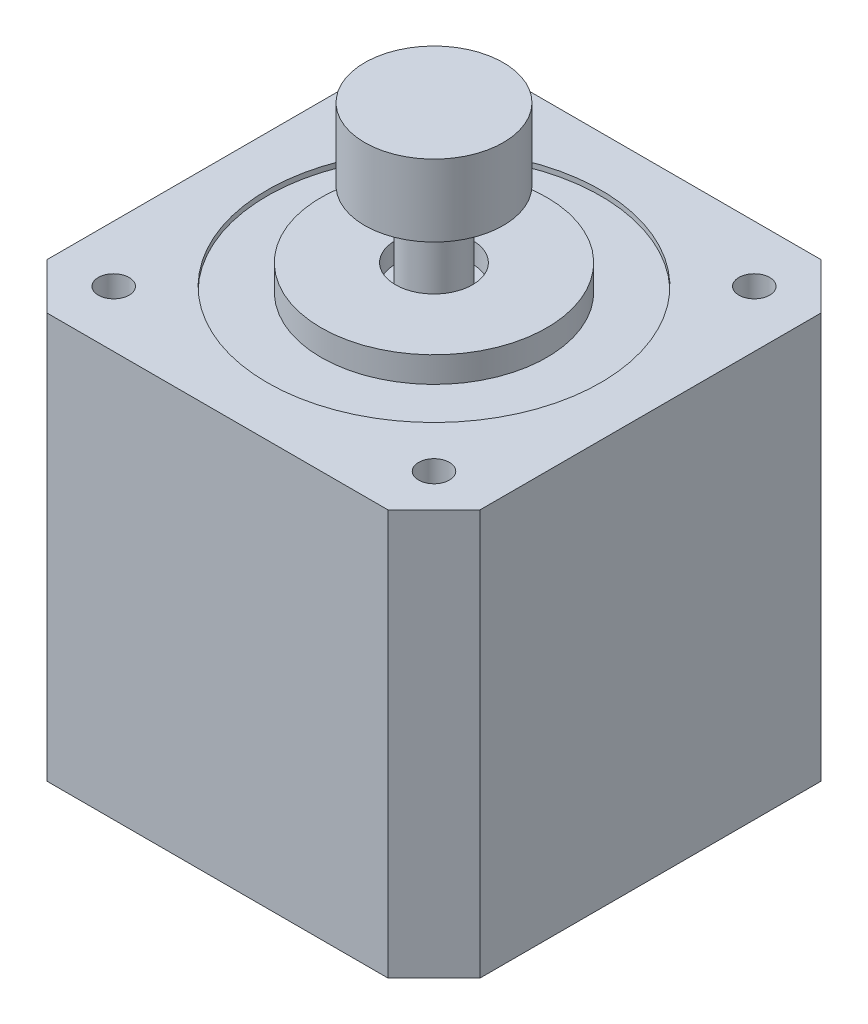
SolidWorks part; units mm, degrees
ref_plane "Alzado" through (0, 0, 0) normal (0, 0, 1) x (1, 0, 0)
ref_plane "Planta" through (0, 0, 0) normal (0, 1, 0) x (1, 0, 0)
ref_plane "Vista lateral" through (0, 0, 0) normal (1, 0, 0) x (0, 0, -1)
sketch "Croquis1" plane through (0, 0, 0) normal (0, 1, 0) x (1, 0, 0)
  line L0 (-16.6, 21.1) -> (-21.1, 16.6)
  line L1 (16.6, 21.1) -> (-16.6, 21.1)
  line L2 (21.1, 16.6) -> (21.1, -16.6)
  line L3 (16.6, -21.1) -> (-16.6, -21.1)
  line L4 (-21.1, 16.6) -> (-21.1, -16.6)
  line L5 (21.1, 21.1) -> (-21.1, -21.1) construction
  line L6 (21.1, -21.1) -> (-21.1, 21.1) construction
  line L7 (21.1, 16.6) -> (16.6, 21.1)
  line L8 (21.1, -16.6) -> (16.6, -21.1)
  line L9 (-16.6, -21.1) -> (-21.1, -16.6)
  point P0 (0, 0)
  dimension "D1" = 42.2
  dimension "D2" = 42.2
  dimension "D3" = 33.2
extrude "Saliente-Extruir1" add sketch "Croquis1" along normal blind 39.5
sketch "Croquis2" plane through (0, 39.5, 0) normal (0, 1, 0) x (1, 0, 0)
  circle A0 centre (0, 0) radius 11
  circle A1 centre (0, 0) radius 3.75
  dimension "D1" = 22
  dimension "D2" = 7.5
extrude "Saliente-Extruir2" add sketch "Croquis2" along normal blind 2
sketch "Croquis3" plane through (0, 39.5, 0) normal (0, 1, 0) x (1, 0, 0)
  circle A0 centre (0, 0) radius 16.25
  circle A1 centre (0, 0) radius 11
  dimension "D1" = 32.5
extrude "Cortar-Extruir2" cut sketch "Croquis3" against normal blind 0.5
sketch "Croquis4" plane through (0, 41.5, 0) normal (0, 1, 0) x (1, 0, 0)
  circle A0 centre (0, 0) radius 2.75
  dimension "D1" = 5.5
extrude "EJE" cut sketch "Croquis4" against normal through all
sketch "Croquis5" plane through (0, 0, 0) normal (0, -1, 0) x (1, 0, 0)
  line L0 (16.6, -21.1) -> (-16.6, -21.1) construction
  line L1 (-21.1, -16.6) -> (-21.1, 16.6) construction
  line L2 (21.1, 16.6) -> (21.1, -16.6) construction
  line L3 (-16.6, 21.1) -> (16.6, 21.1) construction
  circle A0 centre (-15.6, 15.6) radius 3.5
  circle A1 centre (15.6, 15.6) radius 3.5
  circle A2 centre (15.6, -15.6) radius 3.5
  circle A3 centre (-15.6, -15.6) radius 3.5
  dimension "D1" = 5.5
  dimension "D2" = 5.5
  dimension "D3" = 5.5
  dimension "D4" = 5.5
  dimension "D5" = 5.5
  dimension "D6" = 5.5
  dimension "D7" = 5.5
  dimension "D8" = 7
  dimension "D9" = 5.5
  dimension "D10" = 7
  dimension "D11" = 7
  dimension "D12" = 7
extrude "PernosAtras" cut sketch "Croquis5" against normal blind 2
sketch "Croquis6" plane through (0, 39.5, 0) normal (0, 1, 0) x (1, 0, 0)
  line L0 (16.6, 21.1) -> (-16.6, 21.1) construction
  line L1 (21.1, -16.6) -> (21.1, 16.6) construction
  line L2 (-21.1, 16.6) -> (-21.1, -16.6) construction
  line L3 (-16.6, -21.1) -> (16.6, -21.1) construction
  circle A0 centre (-15.6, 15.6) radius 1.5
  circle A1 centre (15.6, 15.6) radius 1.5
  circle A2 centre (15.6, -15.6) radius 1.5
  circle A3 centre (-15.6, -15.6) radius 1.5
  dimension "D1" = 5.5
  dimension "D2" = 3
  dimension "D3" = 5.5
  dimension "D4" = 5.5
  dimension "D5" = 3
  dimension "D6" = 5.5
  dimension "D7" = 5.5
  dimension "D8" = 5.5
  dimension "D9" = 3
  dimension "D10" = 5.5
  dimension "D11" = 5.5
  dimension "D12" = 3
extrude "PernosFrente" cut sketch "Croquis6" against normal blind 5
sketch "Croquis7" plane through (0, 0, 0) normal (0, -1, 0) x (1, 0, 0)
  circle A0 centre (0, 0) radius 2.75
extrude "Saliente-Extruir3" add sketch "Croquis7" against normal blind 55
sketch "Croquis8" plane through (0, 55, 0) normal (0, 1, 0) x (1, 0, 0)
  circle A0 centre (0, 0) radius 6.75
  dimension "D1" = 13.5
extrude "Saliente-Extruir4" add sketch "Croquis8" against normal blind 7
